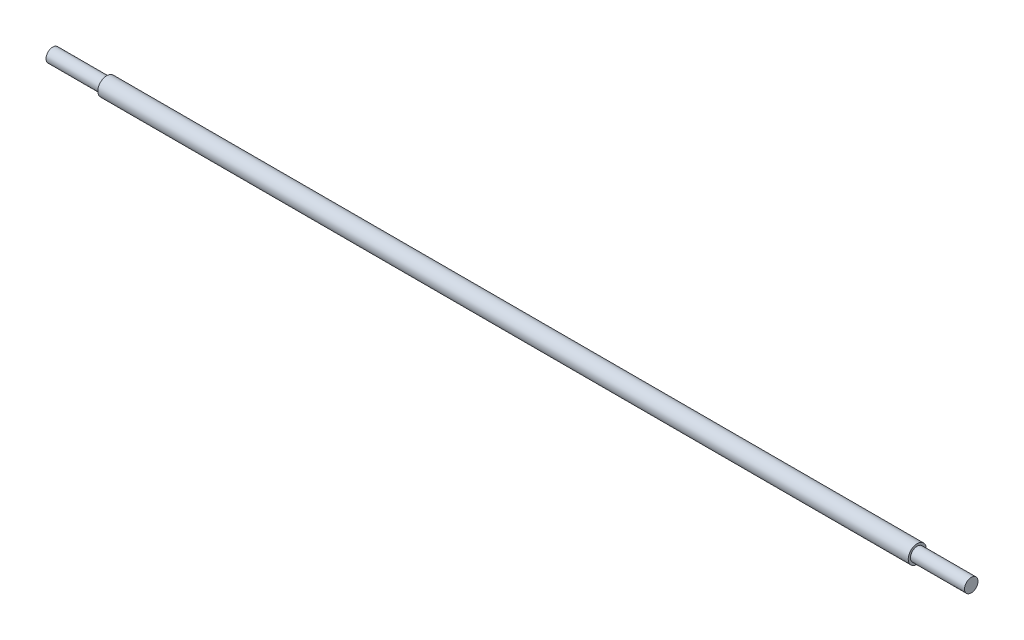
SolidWorks part; units mm, degrees
material "Plain Carbon Steel"
ref_plane "Front Plane" through (0, 0, 0) normal (0, 0, 1) x (1, 0, 0)
ref_plane "Top Plane" through (0, 0, 0) normal (0, 1, 0) x (1, 0, 0)
ref_plane "Right Plane" through (0, 0, 0) normal (1, 0, 0) x (0, 0, -1)
sketch "Sketch2" plane through (0, 0, 0) normal (0, 1, 0) x (1, 0, 0)
  line L0 (-647.7, 0) -> (647.7, 0)
  line L1 (-647.7, 0) -> (-647.7, 9.525)
  line L2 (-647.7, 9.525) -> (-571.5, 9.525)
  line L3 (-571.5, 9.525) -> (-571.5, 12.7)
  line L4 (-571.5, 12.7) -> (571.5, 12.7)
  line L5 (0, 12.7) -> (0, 0) construction
  line L6 (571.5, 9.525) -> (571.5, 12.7)
  line L7 (647.7, 9.525) -> (571.5, 9.525)
  line L8 (647.7, 0) -> (647.7, 9.525)
  point P4 (0, 0)
  dimension "D1" = 1295.4
  dimension "D2" = 9.525
  dimension "D3" = 12.7
  dimension "D4" = 76.2
revolve "Revolve1" add sketch "Sketch2" angle 360 about L0
